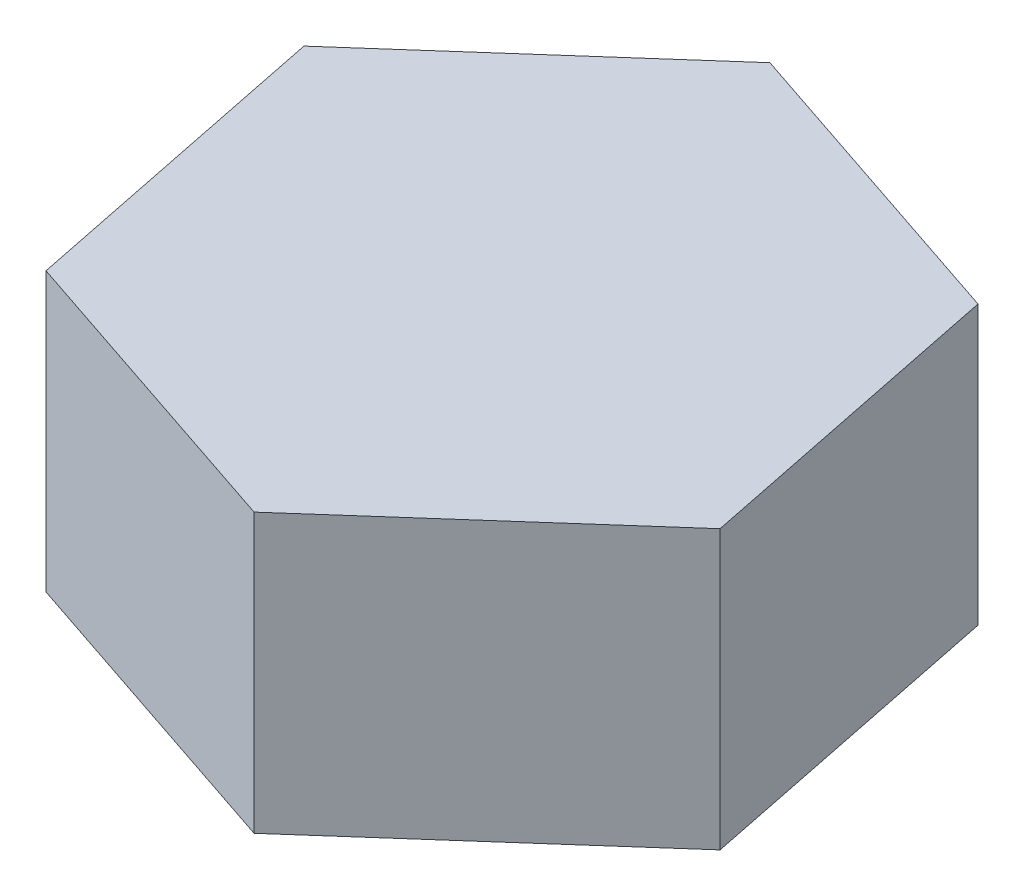
SolidWorks part; units mm, degrees
ref_plane "Front Plane" through (0, 0, 0) normal (0, 0, 1) x (1, 0, 0)
ref_plane "Top Plane" through (0, 0, 0) normal (0, 1, 0) x (1, 0, 0)
ref_plane "Right Plane" through (0, 0, 0) normal (1, 0, 0) x (0, 0, -1)
sketch "Sketch1" plane through (0, 0, 0) normal (0, 1, 0) x (1, 0, 0)
  line L7 (1.6007, 1.4146) -> (-0.4247, 2.0936)
  line L8 (-0.4247, 2.0936) -> (-2.0254, 0.679)
  line L9 (-2.0254, 0.679) -> (-1.6007, -1.4146)
  line L10 (-1.6007, -1.4146) -> (0.4247, -2.0936)
  line L11 (0.4247, -2.0936) -> (2.0254, -0.679)
  line L12 (2.0254, -0.679) -> (1.6007, 1.4146)
  circle A1 centre (0, 0) radius 1.85 construction
  dimension "D2" = 4.2724
extrude "Boss-Extrude1" add sketch "Sketch1" along normal blind 1.8
